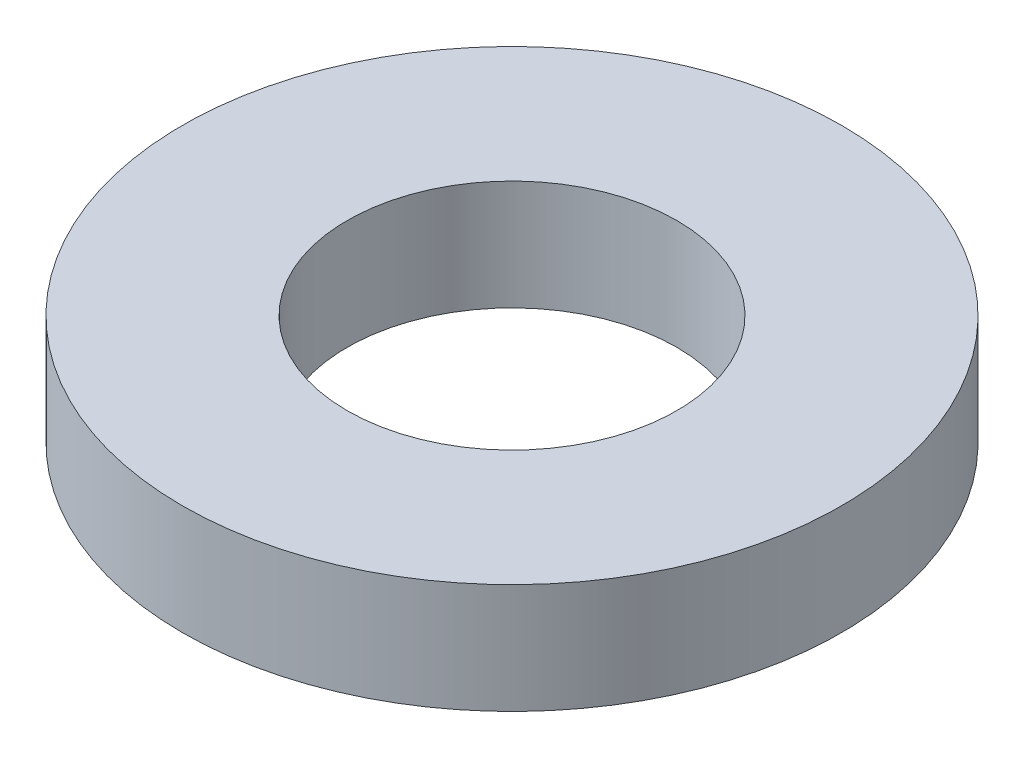
SolidWorks part; units mm, degrees
material "尼龙 101"
ref_plane "前视基准面" through (0, 0, 0) normal (0, 0, 1) x (1, 0, 0)
ref_plane "上视基准面" through (0, 0, 0) normal (0, 1, 0) x (1, 0, 0)
ref_plane "右视基准面" through (0, 0, 0) normal (1, 0, 0) x (0, 0, -1)
sketch "草图1" plane through (0, 0, 0) normal (0, 1, 0) x (1, 0, 0)
  circle A0 centre (0, 0) radius 1.5
  circle A1 centre (0, 0) radius 3
  dimension "D1" = 3
  dimension "D2" = 6
extrude "凸台-拉伸1" add sketch "草图1" along normal blind 1
